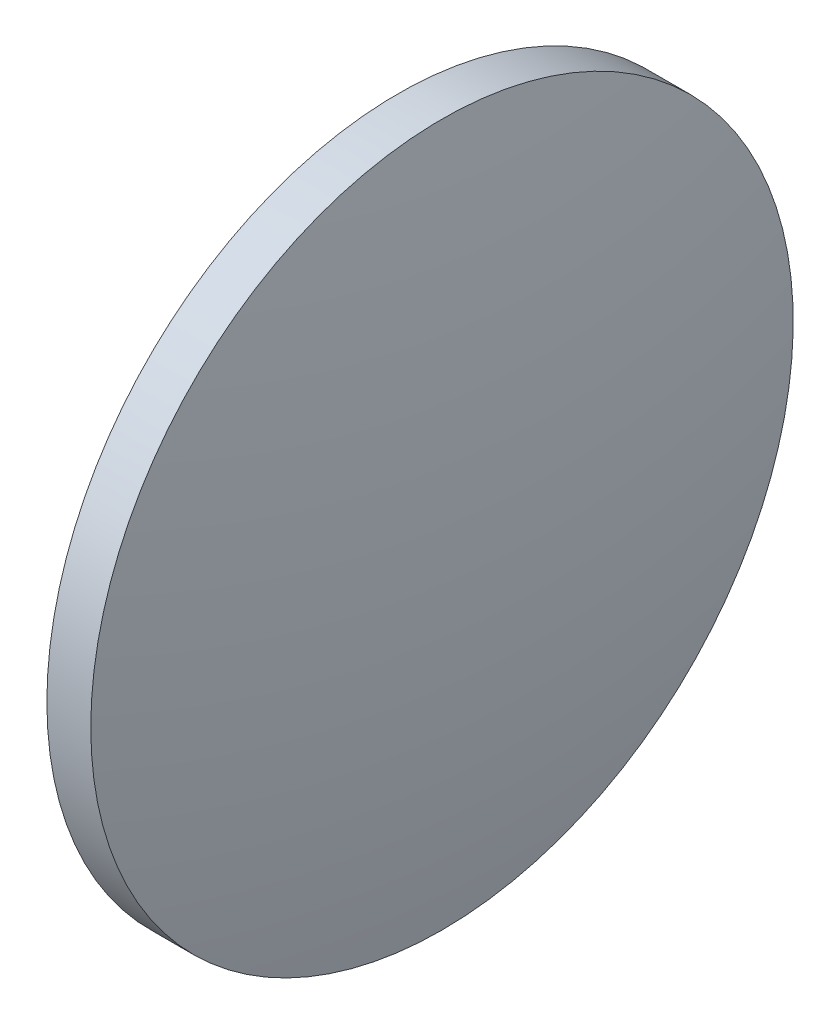
SolidWorks part; units mm, degrees
ref_plane "前视基准面" through (0, 0, 0) normal (0, 0, 1) x (1, 0, 0)
ref_plane "上视基准面" through (0, 0, 0) normal (0, 1, 0) x (1, 0, 0)
ref_plane "右视基准面" through (0, 0, 0) normal (1, 0, 0) x (0, 0, -1)
sketch "草图1" plane through (0, 0, 0) normal (0, 0, 1) x (1, 0, 0)
  line L0 (849.1524, 303.9353) -> (876.0439, 303.9353) construction
  line L1 (858.6589, 303.9353) -> (858.6589, 323.9353)
  line L2 (863.1089, 303.9353) -> (858.6589, 303.9353)
  line L5 (858.6589, 323.9353) -> (861.1589, 323.9353)
  arc A0 (863.1089, 303.9353) -> (861.1589, 323.9353) centre (759.5698, 303.9353) ccw
revolve "旋转1" add sketch "草图1" angle 360 about L0
